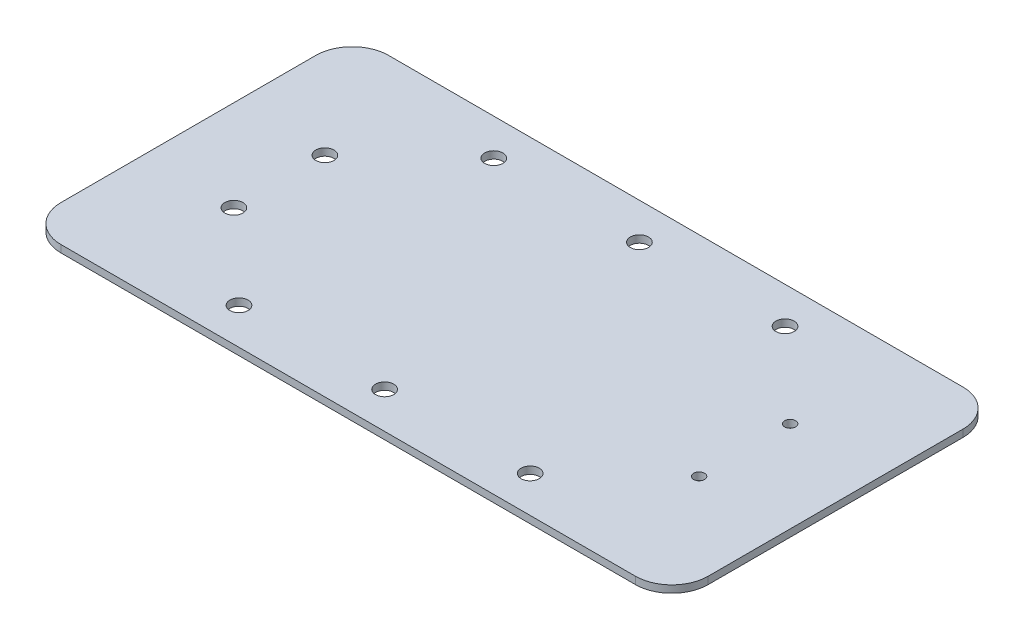
SolidWorks part; units mm, degrees
ref_plane "Front Plane" through (0, 0, 0) normal (0, 0, 1) x (1, 0, 0)
ref_plane "Top Plane" through (0, 0, 0) normal (0, 1, 0) x (1, 0, 0)
ref_plane "Right Plane" through (0, 0, 0) normal (1, 0, 0) x (0, 0, -1)
sketch "Sketch1" plane through (0, 0, 0) normal (0, 1, 0) x (1, 0, 0)
  line L0 (0, -35) -> (0, 35)
  line L1 (-88.9, -45) -> (88.9, -45)
  line L2 (-88.9, -45) -> (-88.9, 45)
  line L3 (-88.9, 45) -> (88.9, 45)
  line L4 (88.9, -45) -> (88.9, 45)
  line L5 (-88.9, -45) -> (88.9, 45) construction
  line L6 (-88.9, 45) -> (88.9, -45) construction
  line L7 (-88.9, 0) -> (88.9, 0) construction
  line L8 (40, -35) -> (40, 35)
  line L9 (-40, -35) -> (-40, 35)
  circle A0 centre (0, 35) radius 2.5
  circle A1 centre (0, -35) radius 2.5
  circle A2 centre (40, 35) radius 2.5
  circle A3 centre (40, -35) radius 2.5
  circle A4 centre (-40, 35) radius 2.5
  circle A5 centre (-40, -35) radius 2.5
  point P0 (0, 0)
  point P9 (0, 0)
  dimension "D4" = 5
  dimension "D1" = 177.8
  dimension "D2" = 90
  dimension "D3" = 70
  dimension "D7" = 40
  dimension "D8" = 40
  dimension "D5" = 2
  dimension "D6" = 2
extrude "Boss-Extrude1" add sketch "Sketch1" along normal blind 2
fillet "Fillet1" radius 10 4 edges at (88.9, 1, 45) (88.9, 1, -45) (-88.9, 1, -45) (-88.9, 1, 45)
sketch "Sketch2" plane through (0, 0, 0) normal (0, -1, 0) x (1, 0, 0)
  line L1 (-78.9, 25) -> (-48.9, 25)
  line L2 (-78.9, 25) -> (-78.9, -25) construction
  line L3 (-78.9, -25) -> (-48.9, -25)
  line L4 (88.9, -35) -> (88.9, 35)
  line L5 (78.9, 45) -> (-78.9, 45)
  line L6 (-88.9, 35) -> (-88.9, -35)
  line L7 (-78.9, -45) -> (78.9, -45)
  line L8 (88.9, -35) -> (88.9, 35)
  line L9 (78.9, 45) -> (-78.9, 45)
  line L10 (-88.9, 35) -> (-88.9, -35)
  line L11 (-78.9, -45) -> (78.9, -45)
  line L12 (-48.9, 25) -> (-48.9, -25)
  line L13 (48.9, 25) -> (78.9, 25)
  line L14 (48.9, 25) -> (48.9, -25)
  line L15 (48.9, -25) -> (78.9, -25)
  line L16 (78.9, 25) -> (78.9, -25)
  line L24 (-78.9, 0) -> (-48.9, 0)
  line L25 (-78.9, 25) -> (-78.9, 0)
  line L26 (0, 45) -> (0, -45)
  circle A0 centre (-63.9, 12.5) radius 2.5
  circle A1 centre (-63.9, -12.5) radius 2.5
  circle A2 centre (63.9, -12.5) radius 1.5
  circle A3 centre (63.9, 12.5) radius 1.5
  arc A4 (88.9, 35) -> (78.9, 45) centre (78.9, 35) ccw
  arc A5 (-78.9, 45) -> (-88.9, 35) centre (-78.9, 35) ccw
  arc A6 (-88.9, -35) -> (-78.9, -45) centre (-78.9, -35) ccw
  arc A7 (78.9, -45) -> (88.9, -35) centre (78.9, -35) ccw
  arc A8 (88.9, 35) -> (78.9, 45) centre (78.9, 35) ccw
  arc A9 (-78.9, 45) -> (-88.9, 35) centre (-78.9, 35) ccw
  arc A10 (-88.9, -35) -> (-78.9, -45) centre (-78.9, -35) ccw
  arc A11 (78.9, -45) -> (88.9, -35) centre (78.9, -35) ccw
  point P20 (-78.9, 0)
  point P21 (-88.9, 0)
  point P22 (48.9, 0)
  point P27 (-78.9, 12.5)
  point P28 (-63.9, 0)
  dimension "D6" = 5
  dimension "D7" = 3
  dimension "D2" = 30
  dimension "D3" = 50
  dimension "D4" = 10
  dimension "D5" = 10
  dimension "D1" = 0
extrude "Cut-Extrude1" cut sketch "Sketch2" against normal up to surface (2 mm away) contours A0 | A1 | A3 | A2 up to face at (0, 2, -32.5)
equation "\"D\"=70"
equation "\"D3@Sketch1\"=\"D\""
